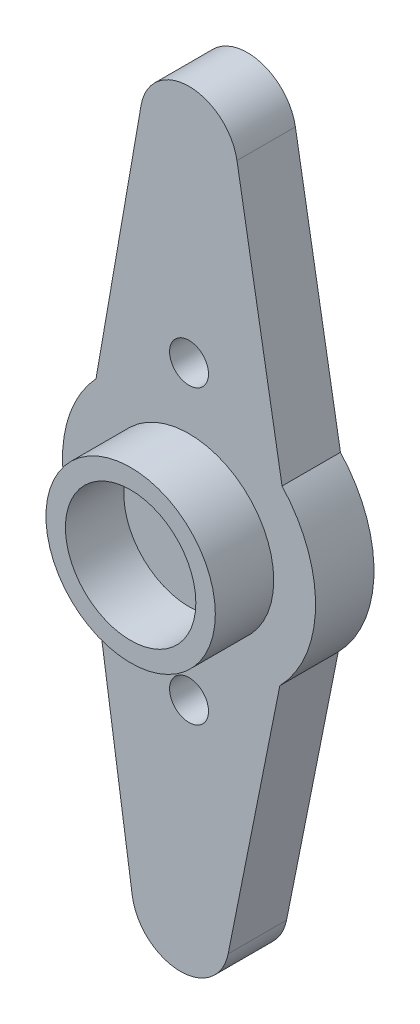
SolidWorks part; units mm, degrees
ref_plane "前视基准面" through (0, 0, 0) normal (0, 0, 1) x (1, 0, 0)
ref_plane "上视基准面" through (0, 0, 0) normal (0, 1, 0) x (1, 0, 0)
ref_plane "右视基准面" through (0, 0, 0) normal (1, 0, 0) x (0, 0, -1)
sketch "草图1" plane through (0, 0, 0) normal (0, 0, 1) x (1, 0, 0)
  line L0 (-2.4631, 17.7279) -> (-4.7773, 4.4077)
  line L1 (0, 29.2442) -> (0, 0) construction
  line L2 (2.4631, 17.7279) -> (4.7773, 4.4077)
  line L3 (2.0093, -17.7851) -> (4.6631, -4.5283)
  line L4 (-2.9153, -17.6592) -> (-4.8883, -4.2842)
  line L5 (-0.7473, -29.2346) -> (-0.506, -19.7935) construction
  line L6 (0, 0) -> (0.0467, 1.8267) construction
  arc A0 (-4.7773, 4.4077) -> (-4.8883, -4.2842) centre (0, 0) ccw
  arc A1 (2.4631, 17.7279) -> (-2.4631, 17.7279) centre (0, 17.3) ccw
  arc A2 (-2.9153, -17.6592) -> (2.0093, -17.7851) centre (-0.4421, -17.2944) ccw
  arc A3 (4.6631, -4.5283) -> (4.7773, 4.4077) centre (0, 0) ccw
  circle A4 centre (0, 7.5) radius 1
  circle A5 centre (0, -7.5) radius 1
  point P18 (0, 0)
  point P25 (0, 0)
  dimension "D1" = 13
  dimension "D2" = 5
  dimension "D5" = 7.5
  dimension "D3" = 17.3
  dimension "D4" = 2
  dimension "D6" = 2
extrude "凸台-拉伸1" add sketch "草图1" along normal blind 3
sketch "草图2" plane through (0, 0, 3) normal (0, 0, 1) x (1, 0, 0)
  circle A0 centre (0, 0) radius 4.35
extrude "拉伸-薄壁1" add sketch "草图2" along normal offset from surface (3 mm away) 6 thin up to face at (1, 7.5, 0) thin type one direction reverse wall 1
